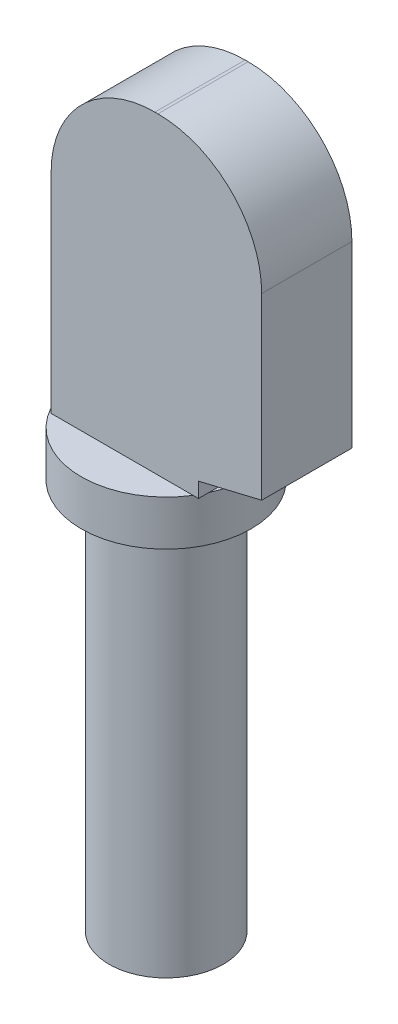
SolidWorks part; units mm, degrees
ref_plane "Front" through (0, 0, 0) normal (0, 0, 1) x (1, 0, 0)
ref_plane "Top" through (0, 0, 0) normal (0, 1, 0) x (1, 0, 0)
ref_plane "Right" through (0, 0, 0) normal (1, 0, 0) x (0, 0, -1)
sketch "Sketch1" plane through (0, 0, 0) normal (0, 0, 1) x (1, 0, 0)
  line L0 (0, 0) -> (0, 22.0717) construction
  line L1 (0, 0) -> (1.9, 0)
  line L2 (1.9, 0) -> (1.9, 13)
  line L3 (1.9, 13) -> (2.825, 13)
  line L4 (2.825, 13) -> (2.825, 14.5)
  line L5 (2.825, 14.5) -> (0, 14.5)
  line L6 (0, 14.5) -> (0, 0)
  dimension "D1" = 3.8
  dimension "D2" = 13
  dimension "D3" = 5.65
  dimension "D4" = 1.5
revolve "Revolve1" add sketch "Sketch1" angle 360 about L0
sketch "Sketch2" plane through (0, 0, 0) normal (0, 0, 1) x (1, 0, 0)
  line L0 (-2.325, 14.5) -> (-2.325, 21.45)
  line L1 (2.825, 14.5) -> (-2.825, 14.5) construction
  line L2 (1.125, 24.9) -> (1.225, 24.9)
  line L3 (4.675, 21.45) -> (4.675, 15.5)
  line L4 (4.675, 15.5) -> (2.575, 15)
  line L5 (2.575, 15) -> (2.575, 14.5)
  line L6 (2.575, 14.5) -> (-2.325, 14.5)
  line L7 (-2.825, 14.5) -> (-2.825, 13) construction
  arc A0 (1.225, 24.9) -> (4.675, 21.45) centre (1.225, 21.45) cw
  arc A1 (-2.325, 21.45) -> (1.125, 24.9) centre (1.125, 21.45) cw
  dimension "D6" = 3.45
  dimension "D7" = 3.45
  dimension "D1" = 0.5
  dimension "D2" = 4.9
  dimension "D3" = 0.5
  dimension "D4" = 7
  dimension "D5" = 10.4
  dimension "D8" = 1
extrude "Boss-Extrude1" add sketch "Sketch2" along normal mid plane 3
